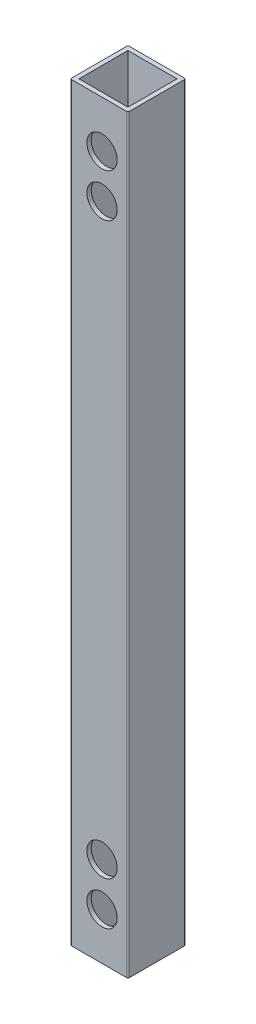
SolidWorks part; units mm, degrees
ref_plane "Front Plane" through (0, 0, 0) normal (0, 0, 1) x (1, 0, 0)
ref_plane "Top Plane" through (0, 0, 0) normal (0, 1, 0) x (1, 0, 0)
ref_plane "Right Plane" through (0, 0, 0) normal (1, 0, 0) x (0, 0, -1)
sketch "Sketch1" plane through (0, 0, 0) normal (0, 1, 0) x (1, 0, 0)
  line L0 (1.5, 1.5) -> (18.5, 1.5)
  line L1 (0.5, 0) -> (19.5, 0)
  line L2 (0, 0.5) -> (0, 19.5)
  line L3 (0.5, 20) -> (19.5, 20)
  line L4 (20, 0.5) -> (20, 19.5)
  line L5 (18.5, 1.5) -> (18.5, 18.5)
  line L6 (1.5, 18.5) -> (18.5, 18.5)
  line L7 (1.5, 1.5) -> (1.5, 18.5)
  arc A0 (19.5, 0) -> (20, 0.5) centre (19.5, 0.5) ccw
  arc A1 (0.5, 0) -> (0, 0.5) centre (0.5, 0.5) cw
  arc A2 (0, 19.5) -> (0.5, 20) centre (0.5, 19.5) cw
  arc A3 (19.5, 20) -> (20, 19.5) centre (19.5, 19.5) cw
  arc A4 (18.5, 1.5) -> (18.5, 1.5) centre (18.5, 1.5) ccw
  arc A5 (18.5, 18.5) -> (18.5, 18.5) centre (18.5, 18.5) cw
  arc A6 (1.5, 18.5) -> (1.5, 18.5) centre (1.5, 18.5) cw
  arc A7 (1.5, 1.5) -> (1.5, 1.5) centre (1.5, 1.5) cw
  point P9 (0, 0)
  dimension "D3" = 0.5
  dimension "D1" = 20
  dimension "D2" = 20
  dimension "D4" = 1.5
extrude "Boss-Extrude1" add sketch "Sketch1" along normal blind 260
sketch "Sketch2" plane through (0, 0, 0) normal (0, 0, 1) x (1, 0, 0)
  line L0 (20, 260) -> (20, 0) construction
  line L1 (19.5, 130) -> (0.5, 130) construction
  line L2 (19.5, 260) -> (19.5, 0) construction
  line L3 (0.5, 260) -> (0.5, 0) construction
  circle A0 centre (11, 243.75) radius 2.65
  circle A1 centre (11, 228.75) radius 2.65
  circle A2 centre (11, 31.25) radius 2.65
  circle A3 centre (11, 16.25) radius 2.65
  dimension "D1" = 15
  dimension "D3" = 5.3
  dimension "D4" = 98.75
  dimension "D2" = 9
extrude "Cut-Extrude1" cut sketch "Sketch2" against normal through all
sketch "Sketch3" plane through (0, 0, 0) normal (0, 0, 1) x (1, 0, 0)
  circle A2 centre (11, 243.75) radius 5.25
  circle A3 centre (11, 228.75) radius 5.25
  circle A4 centre (11, 31.25) radius 5.25
  circle A5 centre (11, 16.25) radius 5.25
  dimension "D1" = 10.5
extrude "Cut-Extrude2" cut sketch "Sketch3" against normal blind 10
